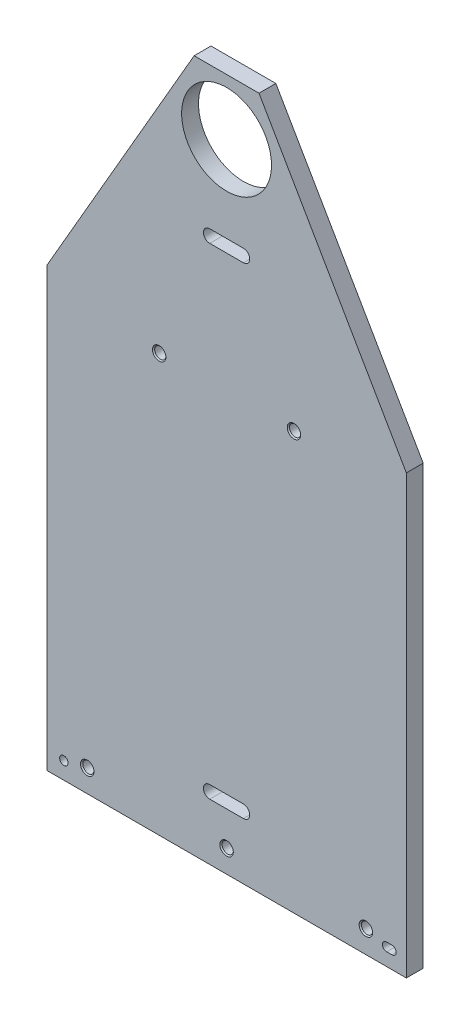
SolidWorks part; units mm, degrees
material "6061-T6 Al"
ref_plane "Front Plane" through (0, 0, 0) normal (0, 0, 1) x (1, 0, 0)
ref_plane "Top Plane" through (0, 0, 0) normal (0, 1, 0) x (1, 0, 0)
ref_plane "Right Plane" through (0, 0, 0) normal (1, 0, 0) x (0, 0, -1)
sketch "Sketch6" plane through (0, 0, 0) normal (0, 0, 1) x (1, 0, 0)
  line L2 (0, 359.7021) -> (0, 0) construction
  line L23 (-101.6, 0) -> (101.6, 0)
  line L24 (-101.6, 0) -> (-101.6, 247.2257)
  line L25 (-18.3309, 391.4521) -> (18.3309, 391.4521)
  line L26 (101.6, 247.2257) -> (101.6, 0)
  line L52 (9.525, 31.9913) -> (-9.525, 31.9913)
  line L53 (9.525, 39.1287) -> (-9.525, 39.1287)
  line L54 (9.525, 304.0253) -> (-9.525, 304.0253)
  line L55 (9.525, 311.1627) -> (-9.525, 311.1627)
  line L56 (9.525, 311.1627) -> (0, 307.594) construction
  line L57 (0, 307.594) -> (-9.525, 304.0253) construction
  line L58 (9.525, 31.9913) -> (0, 35.56) construction
  line L59 (0, 35.56) -> (-9.525, 39.1287) construction
  line L64 (-18.3309, 391.4521) -> (-101.6, 247.2257)
  line L65 (18.3309, 391.4521) -> (101.6, 247.2257)
  line L85 (-53.975, 245.4021) -> (53.975, 245.4021) construction
  line L99 (-53.975, 288.5821) -> (53.975, 288.5821) construction
  line L100 (-57.15, 285.4071) -> (-57.15, 248.5771) construction
  line L101 (-53.975, 58.42) -> (53.975, 58.42) construction
  line L102 (57.15, 285.4071) -> (57.15, 248.5771) construction
  line L103 (-53.975, 194.6021) -> (53.975, 194.6021) construction
  line L104 (-57.15, 191.4271) -> (-57.15, 61.595) construction
  line L105 (57.15, 191.4271) -> (57.15, 61.595) construction
  line L106 (-53.975, 288.5821) -> (-53.975, 391.4521) construction
  line L175 (57.15, 285.4071) -> (101.6, 285.4071) construction
  line L177 (0, 359.7021) -> (0, 391.4521) construction
  line L179 (0, 359.7021) -> (-27.4963, 375.5771) construction
  circle A14 centre (0, 359.7021) radius 25.4
  arc A27 (9.525, 39.1287) -> (9.525, 31.9913) centre (9.525, 35.56) cw
  arc A28 (-9.525, 31.9913) -> (-9.525, 39.1287) centre (-9.525, 35.56) cw
  arc A29 (-9.525, 311.1627) -> (-9.525, 304.0253) centre (-9.525, 307.594) ccw
  arc A30 (9.525, 304.0253) -> (9.525, 311.1627) centre (9.525, 307.594) ccw
  arc A33 (53.975, 245.4021) -> (57.15, 248.5771) centre (53.975, 248.5771) ccw construction
  arc A34 (53.975, 288.5821) -> (57.15, 285.4071) centre (53.975, 285.4071) cw construction
  arc A35 (-53.975, 288.5821) -> (-57.15, 285.4071) centre (-53.975, 285.4071) ccw construction
  arc A36 (-53.975, 245.4021) -> (-57.15, 248.5771) centre (-53.975, 248.5771) cw construction
  arc A37 (53.975, 58.42) -> (57.15, 61.595) centre (53.975, 61.595) ccw construction
  arc A38 (53.975, 194.6021) -> (57.15, 191.4271) centre (53.975, 191.4271) cw construction
  arc A39 (-53.975, 194.6021) -> (-57.15, 191.4271) centre (-53.975, 191.4271) ccw construction
  arc A40 (-57.15, 61.595) -> (-53.975, 58.42) centre (-53.975, 61.595) ccw construction
  dimension "D1" = 50.8
  dimension "D5" = 7.1374
  dimension "D6" = 203.2
  dimension "D7" = 359.7021
  dimension "D9" = 19.05
  dimension "D35" = 71.12
  dimension "D38" = 50.8
  dimension "D39" = 3.175
  dimension "D24" = 35.56
  dimension "D25" = 272.034
  dimension "D40" = 114.3
  dimension "D43" = 30
  dimension "D8" = 31.75
  dimension "D32" = 114.3
  dimension "D36" = 58.42
extrude "Boss-Extrude1" add sketch "Sketch6" against normal mid plane 9.525
hole_wizard "1/4-20 Tapped Hole1" positions "Sketch8" profile "Sketch7" tap size "1/4-20" standard "ANSI Inch" end condition through all
sketch "Sketch8" plane through (-81.7327, 283.4839, 4.7625) normal (0, 0, 1) x (1, 0, 0)
  line L9 (81.7327, 76.2182) -> (81.7327, -47.6068) construction
  point P52 (43.6327, -47.6068)
  point P54 (119.8327, -47.6068)
  dimension "D5" = 123.825
  dimension "D6" = 76.2
sketch "Sketch7" plane through (-38.1, 235.8771, 4.7625) normal (1, 0, 0) x (0, -1, 0)
  line L0 (0, 0) -> (0, 9.525)
  line L1 (0, 9.525) -> (3.81, 9.525)
  line L2 (3.175, 8.89) -> (3.175, 0.635)
  line L3 (3.175, 0.635) -> (3.81, 0)
  line L5 (3.81, 0) -> (0, 0)
  line L6 (-3.175, 0.635) -> (-3.81, 0) construction
  line L7 (3.81, 9.525) -> (3.175, 8.89)
  line L8 (-3.81, 9.525) -> (-3.175, 8.89) construction
  line L11 (0, -6.35) -> (0, 107.95) construction
  dimension "Thread Major Dia." = 6.35
  dimension "Thru Tap Drill Depth" = 9.525
  dimension "Near C'Sink Dia." = 7.62
  dimension "Near C'Sink Angle" = 90
  dimension "Far C'Sink Dia." = 7.62
  dimension "Far C'Sink Angle" = 90
hole_wizard "3/16 (0.1875) Diameter Hole1" positions "Sketch10" profile "Sketch9" hole size "3/16" standard "ANSI Inch" end condition through all
sketch "Sketch10" plane through (643.6501, 199.4195, 4.7625) normal (0, 0, 1) x (1, 0, 0)
  line L15 (-745.2501, -199.4195) -> (-542.0501, -199.4195) construction
  line L17 (-735.5981, -189.7675) -> (-735.5981, -199.4195) construction
  line L23 (-553.2261, -189.7675) -> (-551.7021, -189.7675) construction
  line L24 (-553.2261, -187.3799) -> (-550.1781, -187.3799) construction
  line L25 (-553.2261, -192.1551) -> (-550.1781, -192.1551) construction
  line L43 (-643.6501, 160.2826) -> (-643.6501, -199.4195) construction
  line L44 (-643.6501, 160.2826) -> (-643.6501, -199.4195) construction
  line L45 (-551.7021, -189.7675) -> (-550.1781, -189.7675) construction
  arc A0 (-553.2261, -187.3799) -> (-553.2261, -192.1551) centre (-553.2261, -189.7675) ccw construction
  arc A1 (-550.1781, -192.1551) -> (-550.1781, -187.3799) centre (-550.1781, -189.7675) ccw construction
  point P0 (-735.5981, -189.7675)
  dimension "D4" = 4.7752
  dimension "D1" = 183.896
  dimension "D3" = 9.652
  dimension "D5" = 3.048
sketch "Sketch9" plane through (-91.948, 9.652, 4.7625) normal (1, 0, 0) x (0, -1, 0)
  line L0 (0, 0) -> (0, 9.525)
  line L1 (0, 9.525) -> (2.3876, 9.525)
  line L2 (2.3876, 9.525) -> (2.3876, 0)
  line L5 (2.3876, 0) -> (0, 0)
  line L11 (0, -6.35) -> (0, 107.95) construction
  dimension "Thru Hole Dia." = 4.7752
  dimension "Thru Hole Depth" = 9.525
sketch "Sketch13" plane through (0, 0, 4.7625) normal (0, 0, 1) x (1, 0, 0)
  line L0 (90.424, 9.652) -> (93.472, 9.652) construction
  line L1 (90.424, 12.0396) -> (93.472, 12.0396)
  line L2 (90.424, 7.2644) -> (93.472, 7.2644)
  line L4 (90.424, 7.2644) -> (93.472, 7.2644) construction
  arc A0 (90.424, 12.0396) -> (90.424, 7.2644) centre (90.424, 9.652) ccw
  arc A1 (93.472, 7.2644) -> (93.472, 12.0396) centre (93.472, 9.652) ccw
  arc A4 (90.424, 12.0396) -> (90.424, 7.2644) centre (90.424, 9.652) ccw construction
  point P2 (91.948, 9.652)
extrude "Cut-Extrude1" cut sketch "Sketch13" against normal through all
hole_wizard "1/4-20 Tapped Hole2" positions "Sketch12" profile "Sketch11" tap size "1/4-20" standard "ANSI Inch" end condition through all
sketch "Sketch12" plane through (-6.6617, 408.3162, 4.7625) normal (0, 0, 1) x (1, 0, 0)
  line L8 (98.6097, -398.6642) -> (85.4017, -395.6162) construction
  line L9 (85.4017, -395.6162) -> (-72.0783, -395.6162) construction
  line L11 (-72.0783, -395.6162) -> (-85.2863, -398.6642) construction
  line L25 (-94.9383, -408.3162) -> (108.2617, -408.3162) construction
  point P81 (6.6617, -395.6162)
  point P83 (85.4017, -395.6162)
  point P85 (-72.0783, -395.6162)
  dimension "D1" = 12.7
  dimension "D3" = 157.48
sketch "Sketch11" plane through (0, 12.7, 4.7625) normal (1, 0, 0) x (0, -1, 0)
  line L0 (0, 0) -> (0, 9.525)
  line L1 (0, 9.525) -> (3.81, 9.525)
  line L2 (3.175, 8.89) -> (3.175, 0.635)
  line L3 (3.175, 0.635) -> (3.81, 0)
  line L5 (3.81, 0) -> (0, 0)
  line L6 (-3.175, 0.635) -> (-3.81, 0) construction
  line L7 (3.81, 9.525) -> (3.175, 8.89)
  line L8 (-3.81, 9.525) -> (-3.175, 8.89) construction
  line L11 (0, -6.35) -> (0, 107.95) construction
  dimension "Thread Major Dia." = 6.35
  dimension "Thru Tap Drill Depth" = 9.525
  dimension "Near C'Sink Dia." = 7.62
  dimension "Near C'Sink Angle" = 90
  dimension "Far C'Sink Dia." = 7.62
  dimension "Far C'Sink Angle" = 90
